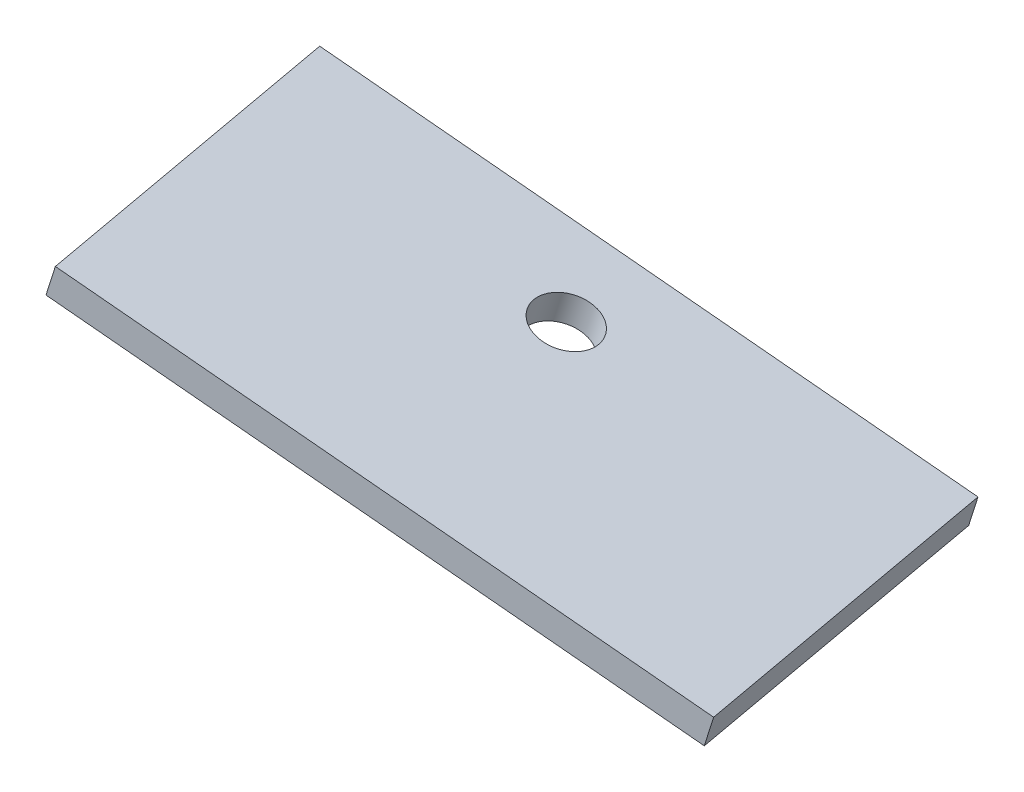
SolidWorks part; units mm, degrees
material "Stainless Steel (ferritic)"
ref_plane "Płaszczyzna XY" through (0, 0, 0) normal (0, 0, 1) x (1, 0, 0)
ref_plane "Płaszczyzna XZ" through (0, 0, 0) normal (0, 1, 0) x (1, 0, 0)
ref_plane "Płaszczyzna YZ" through (0, 0, 0) normal (1, 0, 0) x (0, 0, -1)
sketch "Sketch1" plane through (-2.9149, -10.3353, 0.5288) normal (-0.2711, -0.9613, 0.0492) x (0.9625, -0.2708, 0.0139)
  line L4 (316.5359, 476.0102) -> (356.2203, 468.5216)
  line L5 (356.2203, 468.5216) -> (358.0746, 478.3482)
  line L6 (358.0746, 478.3482) -> (318.3902, 485.8368)
  line L7 (318.3902, 485.8368) -> (316.5359, 476.0102)
  line L8 (316.5359, 476.0102) -> (356.2203, 468.5216)
  line L9 (356.2203, 468.5216) -> (358.0746, 478.3482)
  line L11 (318.3902, 485.8368) -> (316.5359, 476.0102)
  line L468 (318.3902, 485.8368) -> (320.7081, 498.12)
  line L469 (320.7081, 498.12) -> (360.3925, 490.6314)
  line L470 (360.3925, 490.6314) -> (358.0746, 478.3482)
  dimension "D2" = 90
  dimension "D3" = 90
  dimension "D4" = 12.5
  dimension "D1" = 0
extrude "Boss-Extrude1" add sketch "Sketch1" along normal blind 2
sketch "Sketch2" plane through (-3.4572, -12.2579, 0.6271) normal (-0.2711, -0.9613, 0.0492) x (0.9625, -0.2708, 0.0139)
  circle A0 centre (336.7601, 478.2997) radius 2 construction
  circle A1 centre (336.7601, 478.2997) radius 2
extrude "Cut-Extrude1" cut sketch "Sketch2" against normal blind 2
